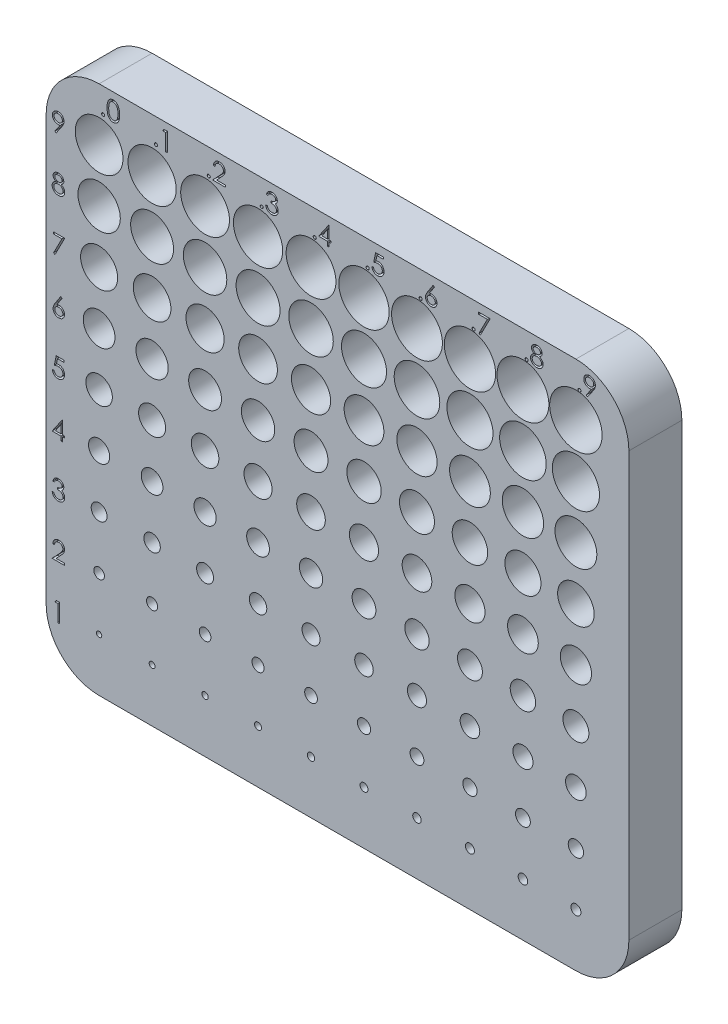
SolidWorks part; units mm, degrees
ref_plane "Ebene vorne" through (0, 0, 0) normal (0, 0, 1) x (1, 0, 0)
ref_plane "Ebene oben" through (0, 0, 0) normal (0, 1, 0) x (1, 0, 0)
ref_plane "Ebene rechts" through (0, 0, 0) normal (1, 0, 0) x (0, 0, -1)
sketch "Skizze1" plane through (0, 0, 0) normal (0, 0, 1) x (1, 0, 0)
  line L1 (-55, -50) -> (55, -50)
  line L2 (-55, -50) -> (-55, 50)
  line L3 (-55, 50) -> (55, 50)
  line L4 (55, -50) -> (55, 50)
  line L5 (-55, -50) -> (55, 50) construction
  line L6 (-55, 50) -> (55, -50) construction
  circle A1 centre (-45, -40) radius 0.5
  circle A2 centre (-45, -30) radius 1
  circle A3 centre (-45, -20) radius 1.5
  circle A4 centre (-45, -10) radius 2
  circle A5 centre (-45, 0) radius 2.5
  circle A6 centre (-45, 10) radius 3
  circle A7 centre (-45, 20) radius 3.5
  circle A8 centre (-45, 30) radius 4
  circle A9 centre (-45, 40) radius 4.5
  circle A10 centre (-35, 40) radius 4.55
  circle A11 centre (-25, 40) radius 4.6
  circle A12 centre (-15, 40) radius 4.65
  circle A13 centre (-5, 40) radius 4.7
  circle A14 centre (5, 40) radius 4.75
  circle A15 centre (15, 40) radius 4.8
  circle A16 centre (25, 40) radius 4.85
  circle A17 centre (35, 40) radius 4.9
  circle A18 centre (45, 40) radius 4.95
  circle A19 centre (45, 30) radius 4.45
  circle A20 centre (45, 20) radius 3.95
  circle A21 centre (45, 10) radius 3.45
  circle A22 centre (45, -10) radius 2.45
  circle A23 centre (45, 0) radius 2.95
  circle A24 centre (45, -40) radius 0.95
  circle A25 centre (45, -30) radius 1.45
  circle A26 centre (45, -20) radius 1.95
  circle A27 centre (-35, -40) radius 0.55
  circle A28 centre (-25, -40) radius 0.6
  circle A29 centre (-15, -40) radius 0.65
  circle A30 centre (-5, -40) radius 0.7
  circle A31 centre (5, -40) radius 0.75
  circle A32 centre (15, -40) radius 0.8
  circle A33 centre (25, -40) radius 0.85
  circle A34 centre (35, -40) radius 0.9
  circle A35 centre (35, -30) radius 1.4
  circle A36 centre (35, -20) radius 1.9
  circle A37 centre (35, -10) radius 2.4
  circle A38 centre (35, 0) radius 2.9
  circle A39 centre (35, 10) radius 3.4
  circle A40 centre (35, 20) radius 3.9
  circle A41 centre (35, 30) radius 4.4
  circle A42 centre (25, 30) radius 4.35
  circle A43 centre (15, 30) radius 4.3
  circle A44 centre (5, 30) radius 4.25
  circle A45 centre (-5, 30) radius 4.2
  circle A46 centre (-15, 30) radius 4.15
  circle A47 centre (-25, 30) radius 4.1
  circle A48 centre (-35, 30) radius 4.05
  circle A49 centre (-35, 20) radius 3.55
  circle A50 centre (-35, 10) radius 3.05
  circle A51 centre (-35, 0) radius 2.55
  circle A52 centre (-35, -10) radius 2.05
  circle A53 centre (-35, -20) radius 1.55
  circle A54 centre (-35, -30) radius 1.05
  circle A55 centre (-25, -30) radius 1.1
  circle A56 centre (-15, -30) radius 1.15
  circle A57 centre (-5, -30) radius 1.2
  circle A58 centre (5, -30) radius 1.25
  circle A59 centre (15, -30) radius 1.3
  circle A60 centre (25, -30) radius 1.35
  circle A61 centre (25, -20) radius 1.85
  circle A62 centre (25, -10) radius 2.35
  circle A63 centre (25, 0) radius 2.85
  circle A64 centre (25, 10) radius 3.35
  circle A65 centre (25, 20) radius 3.85
  circle A66 centre (15, 20) radius 3.8
  circle A67 centre (5, 20) radius 3.75
  circle A68 centre (-5, 20) radius 3.7
  circle A69 centre (-15, 20) radius 3.65
  circle A70 centre (-25, 20) radius 3.6
  circle A71 centre (-25, 10) radius 3.1
  circle A72 centre (-25, 0) radius 2.6
  circle A73 centre (-25, -10) radius 2.1
  circle A74 centre (-25, -20) radius 1.6
  circle A75 centre (-15, -20) radius 1.65
  circle A76 centre (-5, -20) radius 1.7
  circle A77 centre (5, -20) radius 1.75
  circle A78 centre (15, -20) radius 1.8
  circle A79 centre (15, -10) radius 2.3
  circle A80 centre (15, 0) radius 2.8
  circle A81 centre (15, 10) radius 3.3
  circle A82 centre (5, 10) radius 3.25
  circle A83 centre (-5, 10) radius 3.2
  circle A84 centre (-15, 10) radius 3.15
  circle A85 centre (-15, 0) radius 2.65
  circle A86 centre (-15, -10) radius 2.15
  circle A87 centre (-5, -10) radius 2.2
  circle A88 centre (5, -10) radius 2.25
  circle A89 centre (5, 0) radius 2.75
  circle A90 centre (-5, 0) radius 2.7
  point P0 (0, 0)
  point P6 (-45, -40)
  point P7 (-35, -40)
  point P8 (-35, -30)
  point P9 (-25, -40)
  point P10 (-15, -40)
  point P11 (-5, -40)
  point P12 (5, -40)
  point P13 (15, -40)
  point P14 (25, -40)
  point P15 (35, -40)
  point P16 (45, -40)
  point P17 (-35, -20)
  point P18 (-45, -30)
  point P19 (-45, -20)
  point P20 (-45, -10)
  point P21 (-45, 0)
  point P22 (-45, 10)
  point P23 (-45, 20)
  point P24 (-45, 30)
  point P25 (-45, 40)
  point P26 (-25, -30)
  point P27 (-15, -30)
  point P28 (-5, -30)
  point P29 (5, -30)
  point P30 (15, -30)
  point P31 (25, -30)
  point P32 (35, -30)
  point P33 (45, -30)
  point P34 (-35, -10)
  point P36 (-35, 0)
  point P37 (-35, 10)
  point P38 (-35, 20)
  point P39 (-35, 30)
  point P40 (-35, 40)
  point P41 (-25, -20)
  point P42 (-25, -10)
  point P43 (-25, 0)
  point P44 (-25, 10)
  point P45 (-25, 20)
  point P46 (-25, 30)
  point P47 (-25, 40)
  point P48 (-15, -20)
  point P49 (-15, -10)
  point P50 (-15, 0)
  point P51 (-15, 10)
  point P52 (-15, 20)
  point P53 (-15, 30)
  point P54 (-15, 40)
  point P55 (-5, -20)
  point P56 (-5, -10)
  point P57 (-5, 0)
  point P58 (-5, 10)
  point P59 (-5, 20)
  point P60 (-5, 30)
  point P61 (-5, 40)
  point P62 (5, -20)
  point P63 (5, -10)
  point P64 (5, 0)
  point P65 (5, 10)
  point P66 (5, 20)
  point P67 (5, 30)
  point P68 (5, 40)
  point P69 (15, -20)
  point P70 (15, -10)
  point P71 (15, 0)
  point P72 (15, 10)
  point P73 (15, 20)
  point P74 (15, 30)
  point P75 (15, 40)
  point P76 (25, -20)
  point P77 (25, -10)
  point P78 (25, 0)
  point P79 (25, 10)
  point P80 (25, 20)
  point P81 (25, 30)
  point P82 (25, 40)
  point P83 (35, -20)
  point P84 (35, -10)
  point P85 (35, 0)
  point P86 (35, 10)
  point P87 (35, 20)
  point P88 (35, 30)
  point P89 (35, 40)
  point P90 (45, -20)
  point P91 (45, -10)
  point P92 (45, 0)
  point P93 (45, 10)
  point P94 (45, 20)
  point P95 (45, 30)
  point P96 (45, 40)
  dimension "D9" = 1
  dimension "D10" = 2
  dimension "D11" = 3
  dimension "D12" = 4
  dimension "D13" = 5
  dimension "D1" = 110
  dimension "D2" = 100
  dimension "D3" = 10
  dimension "D4" = 10
  dimension "D5" = 10
  dimension "D6" = 9
  dimension "D7" = 10
  dimension "D8" = 10
extrude "Aufsatz-Linear austragen2" add sketch "Skizze1" along normal blind 10
sketch "Skizze4" plane through (0, 0, 10) normal (0, 0, 1) x (1, 0, 0)
  line L0 (55, 50) -> (-55, 50) construction
  line L1 (-55, 50) -> (-55, -50) construction
  point P0 (-45, 45)
  point P5 (0, 0)
  point P6 (0, 0)
  point P7 (-35, 45)
  point P8 (-25, 45)
  point P9 (-15, 45)
  point P10 (-5, 45)
  point P11 (5, 45)
  point P12 (15, 45)
  point P13 (25, 45)
  point P14 (35, 45)
  point P15 (45, 45)
  dimension "D1" = 5
  dimension "D2" = 10
  dimension "D3" = 10
sketch "Skizze6" plane through (0, 0, 10) normal (0, 0, 1) x (1, 0, 0)
  line L0 (-55, -50) -> (55, -50) construction
  line L1 (-55, 50) -> (-55, -50) construction
  text T0 ".0"
  text T1 ".1"
  text T2 ".2\r\n"
  text T3 ".3\r\n"
  text T4 ".4\r\n"
  text T5 ".5\r\n"
  text T6 ".6\r\n"
  text T7 ".7"
  text T8 ".8\r\n"
  text T9 ".9"
  text T10 "1"
  text T11 "2"
  text T12 "3\r\n"
  text T13 "4"
  text T14 "5"
  text T15 "6"
  text T16 "7"
  text T17 "8"
  text T18 "9"
  point P12 (-54, -42)
  point P14 (-54, -32)
  point P15 (-54, -22)
  point P16 (-54, -12)
  point P20 (-54, -2)
  point P21 (-54, 8)
  point P22 (-54, 18)
  point P23 (-54, 28)
  point P24 (-54, 38)
  point P31 (-54, 28)
  dimension "D1" = 8
  dimension "D2" = 1
  dimension "D3" = 9
extrude "Schnitt-Linear austragen3" cut sketch "Skizze6" against normal blind 1
fillet "Verrundung1" radius 10 4 edges at (55, 50, 5) (-55, -50, 5) (55, -50, 5) (-55, 50, 5)
